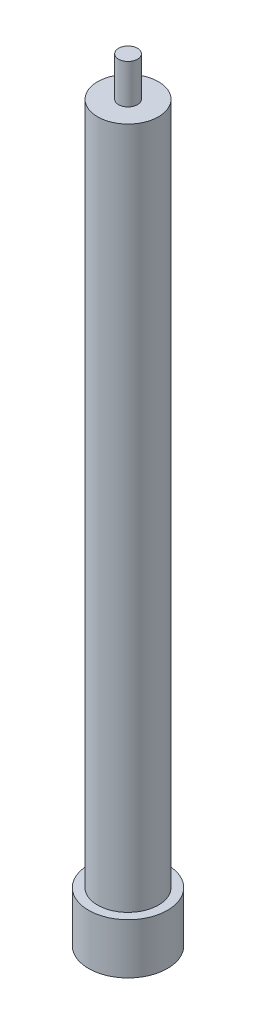
SolidWorks part; units mm, degrees
ref_plane "Front Plane" through (0, 0, 0) normal (0, 0, 1) x (1, 0, 0)
ref_plane "Top Plane" through (0, 0, 0) normal (0, 1, 0) x (1, 0, 0)
ref_plane "Right Plane" through (0, 0, 0) normal (1, 0, 0) x (0, 0, -1)
sketch "Sketch1" plane through (0, 0, 0) normal (0, 1, 0) x (1, 0, 0)
  circle A0 centre (0, 0) radius 24.511
  circle A1 centre (0, 0) radius 7.62
extrude "Boss-Extrude1" add sketch "Sketch1" along normal blind 622.3 contours A1
sketch "Sketch2" plane through (0, 0, 0) normal (0, -1, 0) x (1, 0, 0)
  circle A0 centre (0, 0) radius 24.511
extrude "Boss-Extrude2" add sketch "Sketch2" against normal blind 590.55
sketch "Sketch3" plane through (0, 0, 0) normal (0, -1, 0) x (1, 0, 0)
  circle A0 centre (0, 0) radius 31.75
extrude "Boss-Extrude3" add sketch "Sketch3" against normal blind 40.64
